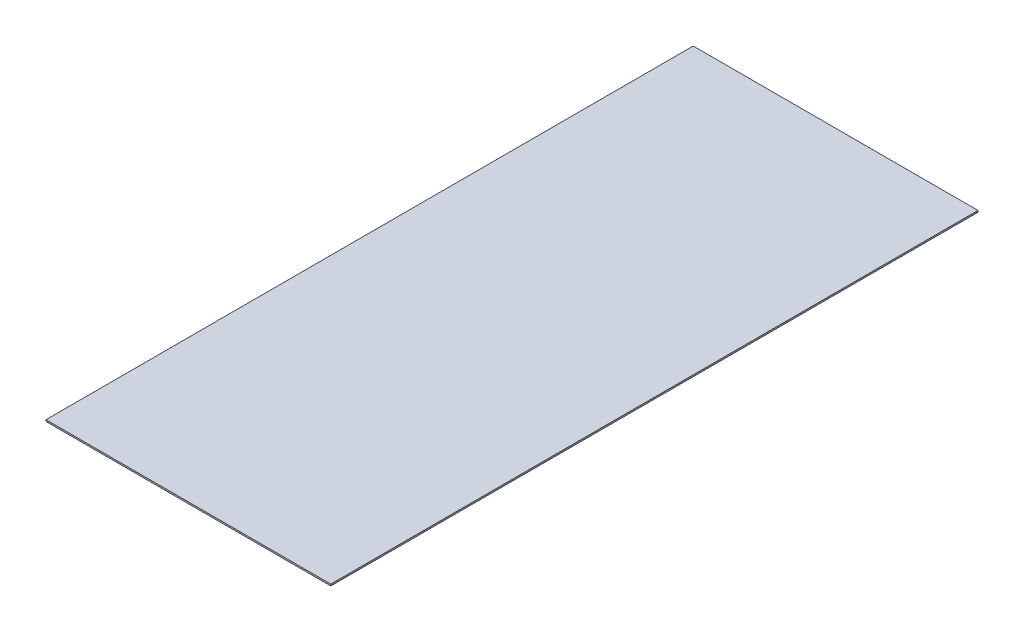
SolidWorks part; units mm, degrees
ref_plane "Front Plane" through (0, 0, 0) normal (0, 0, 1) x (1, 0, 0)
ref_plane "Top Plane" through (0, 0, 0) normal (0, 1, 0) x (1, 0, 0)
ref_plane "Right Plane" through (0, 0, 0) normal (1, 0, 0) x (0, 0, -1)
sketch "Sketch1" plane through (0, 0, 0) normal (0, 0, 1) x (1, 0, 0)
  line L1 (-139.7, -0.7937) -> (139.7, -0.7937)
  line L2 (-139.7, -0.7937) -> (-139.7, 0.7938)
  line L3 (-139.7, 0.7938) -> (139.7, 0.7938)
  line L4 (139.7, -0.7937) -> (139.7, 0.7938)
  line L5 (-139.7, -0.7937) -> (139.7, 0.7938) construction
  line L6 (-139.7, 0.7938) -> (139.7, -0.7937) construction
  point P0 (0, 0)
  dimension "D1" = 1.5875
  dimension "D2" = 279.4
extrude "Boss-Extrude1" add sketch "Sketch1" along normal blind 635
